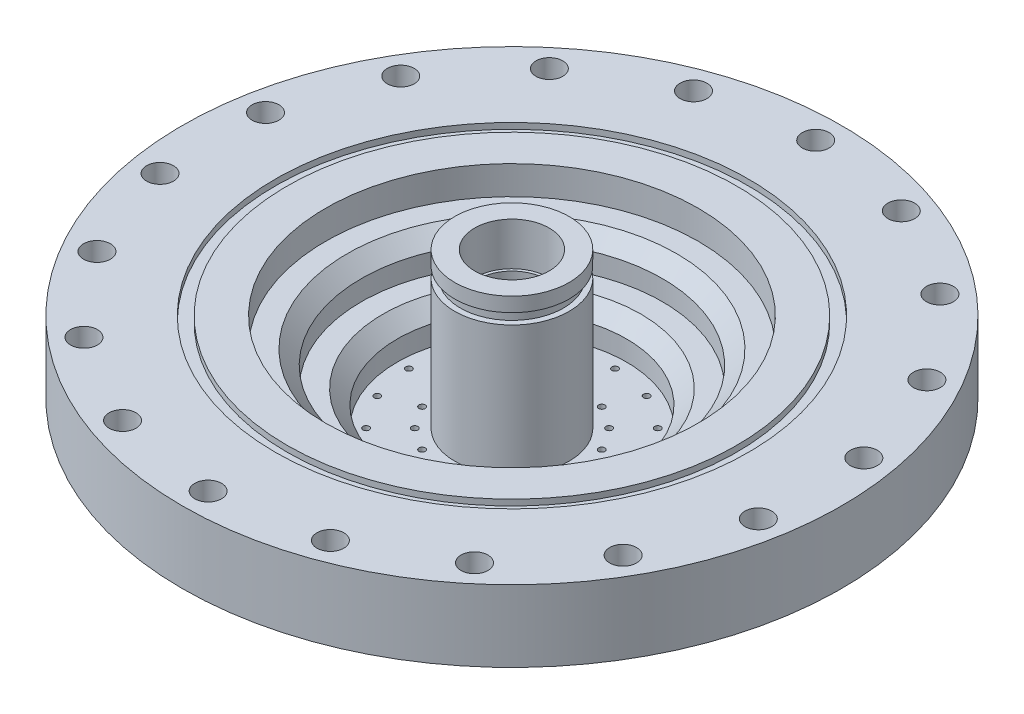
SolidWorks part; units mm, degrees
material "6061-T4 (SS)"
ref_plane "Front Plane" through (0, 0, 0) normal (0, 0, 1) x (1, 0, 0)
ref_plane "Top Plane" through (0, 0, 0) normal (0, 1, 0) x (1, 0, 0)
ref_plane "Right Plane" through (0, 0, 0) normal (1, 0, 0) x (0, 0, -1)
sketch "Sketch1" plane through (0, 0, 0) normal (0, 1, 0) x (1, 0, 0)
  circle A0 centre (0, 0) radius 38.0746
  dimension "D1" = 76.1492
extrude "Boss-Extrude1" add sketch "Sketch1" along normal blind 4.445
sketch "Sketch2" plane through (0, 4.445, 0) normal (0, 1, 0) x (1, 0, 0)
  circle A0 centre (0, 0) radius 28.575
  circle A1 centre (0, 0) radius 7.62
  dimension "D1" = 57.15
  dimension "D2" = 15.24
extrude "Boss-Extrude2" add sketch "Sketch2" along normal blind 5.08
sketch "Sketch4" plane through (0, 9.525, 0) normal (0, 1, 0) x (1, 0, 0)
  circle A0 centre (0, 0) radius 38.0746
  circle A1 centre (0, 0) radius 7.62
  circle A2 centre (0, 0) radius 7.62 construction
  dimension "D1" = 76.1492
extrude "Boss-Extrude3" add sketch "Sketch4" along normal blind 25.4
sketch "Sketch5" plane through (0, 34.925, 0) normal (0, 1, 0) x (1, 0, 0)
  circle A0 centre (0, 0) radius 73.025
  circle A1 centre (0, 0) radius 38.0746
  circle A2 centre (0, 0) radius 38.0746 construction
  dimension "D1" = 146.05
extrude "Boss-Extrude4" add sketch "Sketch5" against normal blind 19.05
sketch "Sketch6" plane through (0, 34.925, 0) normal (0, 1, 0) x (1, 0, 0)
  circle A0 centre (0, 0) radius 41.275
  circle A1 centre (0, 0) radius 12.6746
  dimension "D1" = 25.3492
  dimension "D2" = 82.55
extrude "Cut-Extrude1" cut sketch "Sketch6" against normal blind 9.525
sketch "Sketch7" plane through (0, 25.4, 0) normal (0, 1, 0) x (1, 0, 0)
  circle A0 centre (0, 0) radius 12.6746
  circle A1 centre (0, 0) radius 33.3375
  circle A2 centre (0, 0) radius 12.6746 construction
  dimension "D1" = 66.675
extrude "Cut-Extrude2" cut sketch "Sketch7" against normal blind 7.62
sketch "Sketch8" plane through (0, 17.78, 0) normal (0, 1, 0) x (1, 0, 0)
  circle A0 centre (0, 0) radius 12.6746
  circle A1 centre (0, 0) radius 25.4
  circle A2 centre (0, 0) radius 12.6746 construction
  dimension "D1" = 50.8
extrude "Cut-Extrude3" cut sketch "Sketch8" against normal blind 7.62
sketch "Sketch9" plane through (0, 0, 0) normal (0, 0, 1) x (1, 0, 0)
  line L0 (0, 0) -> (0, 34.925) construction
  line L1 (7.62, 34.925) -> (-7.62, 34.925) construction
  line L2 (7.62, 4.445) -> (-7.62, 4.445) construction
  circle A0 centre (0, 6.985) radius 1.5875
  dimension "D2" = 3.175
  dimension "D1" = 2.54
sketch "Sketch10" plane through (0, 34.925, 0) normal (0, 1, 0) x (1, 0, 0)
  circle A0 centre (0, 0) radius 12.6746
  circle A1 centre (0, 0) radius 8.255
  circle A3 centre (0, 0) radius 12.6746 construction
  dimension "D1" = 16.51
extrude "Boss-Extrude5" add sketch "Sketch10" along normal blind 9.525
sketch "Sketch11" plane through (0, 0, 0) normal (0, 0, 1) x (1, 0, 0)
  line L0 (0, 0) -> (-38.0746, 0) construction
  line L1 (-38.0746, 0) -> (38.0746, 0) construction
  line L2 (-38.0746, 0) -> (-38.0746, 4.445) construction
  line L3 (38.0746, 4.445) -> (-38.0746, 4.445) construction
  line L4 (-38.0746, 2.2225) -> (-36.83, 2.2225) construction
  line L5 (-36.83, 3.4036) -> (-36.83, 1.0414)
  line L6 (-36.83, 3.4036) -> (-38.0746, 3.4036)
  line L7 (-36.83, 1.0414) -> (-38.0746, 1.0414)
  line L8 (-38.0746, 3.4036) -> (-38.0746, 1.0414)
  line L9 (0, 0) -> (0, 24.1447) construction
  point P10 (-36.83, 2.2225)
  dimension "D1" = 38.0746
  dimension "D2" = 36.83
  dimension "D3" = 2.3622
chamfer "Chamfer1" distance 3.175 angle 45 2 edges at (0, 17.78, 25.4) (0, 25.4, 33.3375)
sketch "Sketch12" plane through (0, 0, 0) normal (0, -1, 0) x (1, 0, 0)
  line L0 (0, 0) -> (0, 38.0746) construction
  line L1 (0, 0) -> (14.5705, 35.1763) construction
  line L2 (14.5705, 35.1763) -> (11.6564, 28.1411) construction
  line L3 (11.6564, 28.1411) -> (8.7423, 21.1058) construction
  line L4 (8.7423, 21.1058) -> (5.8282, 14.0705) construction
  line L5 (5.8282, 14.0705) -> (2.9141, 7.0353) construction
  line L6 (2.9141, 7.0353) -> (0, 0) construction
  circle A0 centre (0, 0) radius 38.0746 construction
  circle A1 centre (5.8282, 14.0705) radius 0.6985
  circle A2 centre (8.7423, 21.1058) radius 0.6985
  dimension "D2" = 1.397
  dimension "D1" = 22.5
  dimension "D3" = 38.0746
extrude "Cut-Extrude5" cut sketch "Sketch12" against normal up to next (10.16 mm away)
ref_plane "Plane1" through (0, 0, 0) normal (-0.9239, 0, 0.3827) x (0.3827, 0, 0.9239)
sketch "Sketch13" plane through (0, 0, 0) normal (-0.9239, 0, 0.3827) x (0.3827, 0, 0.9239)
  line L0 (7.6149, 0) -> (4.4269, 5.5217)
  line L1 (30.4597, 0) -> (34.3765, 6.7842)
  line L2 (0, 0) -> (38.0746, 0) construction
  line L3 (30.4597, 0) -> (22.8448, 0) construction
  line L4 (30.4597, 0) -> (26.107, -7.539) construction
  line L5 (7.6149, 0) -> (11.9676, -7.539)
  line L6 (22.5375, -1.4364) -> (1.3976, -13.6416) construction
  line L7 (37.4085, -14.0639) -> (14.8055, -1.0141) construction
  point P15 (11.9676, -7.539)
  point P18 (26.107, -7.539)
  dimension "D1" = 60
  dimension "D2" = 60
ref_plane "Plane2" through (2.3942, -10.8364, 5.7801) normal (-0.1913, 0.866, -0.4619) x (-0.3314, -0.5, -0.8001)
sketch "Sketch14" plane through (2.3942, -10.8364, 5.7801) normal (-0.1913, 0.866, -0.4619) x (-0.3314, -0.5, -0.8001)
  circle A0 centre (-6.5947, 0) radius 0.508
  dimension "D1" = 1.016
extrude "Cut-Extrude6" cut sketch "Sketch14" along normal up to next
ref_plane "Plane3" through (1.2484, 5.6504, 3.014) normal (0.1913, 0.866, 0.4619) x (-0.3314, 0.5, -0.8001)
sketch "Sketch15" plane through (1.2484, 5.6504, 3.014) normal (0.1913, 0.866, 0.4619) x (-0.3314, 0.5, -0.8001)
  circle A0 centre (-26.3789, 0) radius 0.508
  dimension "D1" = 1.016
extrude "Cut-Extrude7" cut sketch "Sketch15" along normal up to next
pattern_circular "CirPattern2" count 16 over 360 about axis through (0, 0, 0) along (0, 1, 0) of "Cut-Extrude5", "Cut-Extrude6", "Cut-Extrude7"
sketch "Sketch16" plane through (0, 0, 0) normal (0, 0, 1) x (1, 0, 0)
  line L0 (0, 0) -> (0, 44.45) construction
  line L1 (-38.0746, 0) -> (38.0746, 0) construction
  line L2 (8.255, 44.45) -> (-8.255, 44.45) construction
  line L3 (0, 44.45) -> (-12.7, 44.45) construction
  line L4 (12.6746, 44.45) -> (-12.6746, 44.45) construction
  line L9 (-12.7, 44.45) -> (-12.7, 41.275) construction
  line L11 (-12.7, 41.275) -> (-11.43, 41.275)
  line L12 (-12.7, 41.275) -> (-12.7, 38.9128)
  line L13 (-12.7, 38.9128) -> (-11.43, 38.9128)
  line L14 (-11.43, 41.275) -> (-11.43, 38.9128)
  dimension "D1" = 12.7
  dimension "D2" = 3.175
  dimension "D3" = 22.86
  dimension "D4" = 2.3622
revolve "Cut-Revolve2" cut sketch "Sketch16" angle 360 about L0
sketch "Sketch17" plane through (0, 34.925, 0) normal (0, 1, 0) x (1, 0, 0)
  circle A0 centre (0, 0) radius 67.31 construction
  circle A1 centre (0, 67.31) radius 2.9769
  dimension "D1" = 134.62
  dimension "D2" = 5.9538
extrude "Cut-Extrude8" cut sketch "Sketch17" against normal through all
pattern_circular "CirPattern3" count 18 over 360 about axis through (0, 0, 0) along (0, 1, 0) of "Cut-Extrude8"
sketch "Sketch20" plane through (0, 34.925, 0) normal (0, 1, 0) x (1, 0, 0)
  circle A0 centre (0, 0) radius 86.431
  circle A1 centre (0, 0) radius 37.2213
extrude "Cut-Extrude11" cut sketch "Sketch20" against normal blind 3.175
sketch "Sketch18" plane through (0, 31.75, 0) normal (0, 1, 0) x (1, 0, 0)
  circle A0 centre (0, 0) radius 49.7967
  circle A1 centre (0, 0) radius 52.4383
  circle A3 centre (0, 0) radius 41.275 construction
  dimension "D1" = 2.6416
  dimension "D2" = 104.8766
extrude "Cut-Extrude9" cut sketch "Sketch18" against normal blind 1.3208
ref_plane "Plane4" through (0, 0, 0) normal (0.9808, 0, -0.1951) x (0, 1, 0)
sketch "Sketch19" plane through (0, 0, 0) normal (0.9808, 0, -0.1951) x (0, 1, 0)
  line L0 (0, 0) -> (9.8103, 0) construction
  circle A0 centre (6.35, 0) radius 0.7938
  dimension "D1" = 1.5875
  dimension "D2" = 6.35
extrude "Cut-Extrude10" cut sketch "Sketch19" against normal through all
pattern_circular "CirPattern4" count 16 over 360 about axis through (0, 15.875, 0) along (0, 1, 0) of "Cut-Extrude10"
sketch "Sketch21" plane through (0, 0, 0) normal (0, 0, 1) x (1, 0, 0)
  line L0 (0, 0) -> (0, 49.8913) construction
  line L1 (0, 0) -> (38.0746, 0) construction
  line L2 (-38.0746, 0) -> (38.0746, 0) construction
  line L3 (38.0746, 0) -> (38.0746, 4.445) construction
  line L4 (38.0746, 4.445) -> (-38.0746, 4.445) construction
  line L6 (39.3192, 3.4036) -> (36.83, 3.4036)
  line L7 (39.3192, 3.4036) -> (39.3192, 1.0414)
  line L8 (39.3192, 1.0414) -> (36.83, 1.0414)
  line L9 (36.83, 3.4036) -> (36.83, 1.0414)
  line L10 (39.3192, 3.4036) -> (36.83, 1.0414) construction
  line L11 (39.3192, 1.0414) -> (36.83, 3.4036) construction
  point P9 (38.0746, 2.2225)
  dimension "D1" = 76.1492
  dimension "D2" = 73.66
  dimension "D3" = 2.3622
